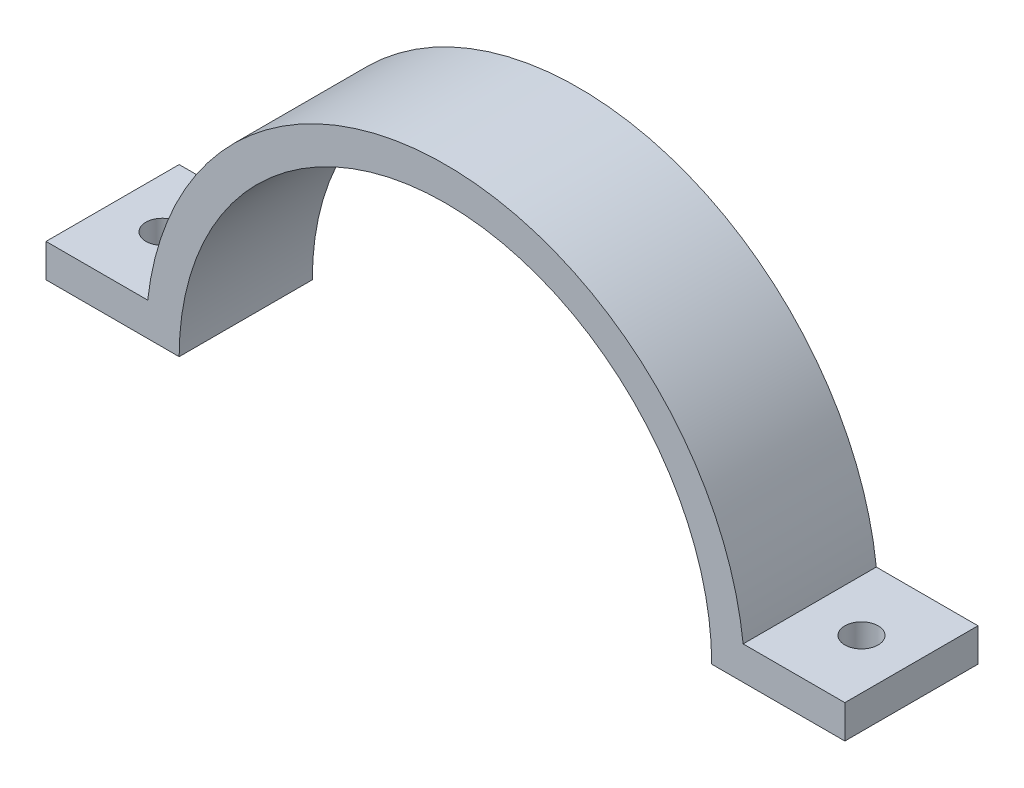
SolidWorks part; units mm, degrees
ref_plane "Front Plane" through (0, 0, 0) normal (0, 0, 1) x (1, 0, 0)
ref_plane "Top Plane" through (0, 0, 0) normal (0, 1, 0) x (1, 0, 0)
ref_plane "Right Plane" through (0, 0, 0) normal (1, 0, 0) x (0, 0, -1)
sketch "Sketch1" plane through (0, 0, 0) normal (0, 0, 1) x (1, 0, 0)
  line L0 (-45, 0) -> (-40, 0)
  line L1 (40, 0) -> (45, 0)
  line L2 (-45, 0) -> (-60, 0)
  line L3 (-60, 0) -> (-60, 5)
  line L4 (-60, 5) -> (-44.7214, 5)
  line L5 (60, 5) -> (60, 0)
  line L6 (60, 0) -> (45, 0)
  line L7 (44.7214, 5) -> (60, 5)
  arc A0 (40, 0) -> (-40, 0) centre (0, 0) ccw
  arc A1 (44.7214, 5) -> (-44.7214, 5) centre (0, 0) ccw
  dimension "D1" = 40
  dimension "D3" = 45
  dimension "D2" = 15
  dimension "D4" = 15
  dimension "D5" = 5
extrude "Boss-Extrude1" add sketch "Sketch1" along normal blind 20
sketch "Sketch3" plane through (0, 5, 0) normal (0, 1, 0) x (1, 0, 0)
  line L0 (-44.7214, 0) -> (-60, 0) construction
  line L1 (60, 0) -> (44.7214, 0) construction
  line L2 (-60, -20) -> (-60, 0) construction
  line L4 (60, -20) -> (60, 0) construction
  circle A0 centre (-52.5, -10) radius 2.5
  circle A1 centre (52.5, -10) radius 2.5
  dimension "D1" = 5
  dimension "D2" = 5
  dimension "D3" = 10
  dimension "D4" = 10
  dimension "D5" = 7.5
  dimension "D6" = 7.5
extrude "Cut-Extrude2" cut sketch "Sketch3" against normal through all
